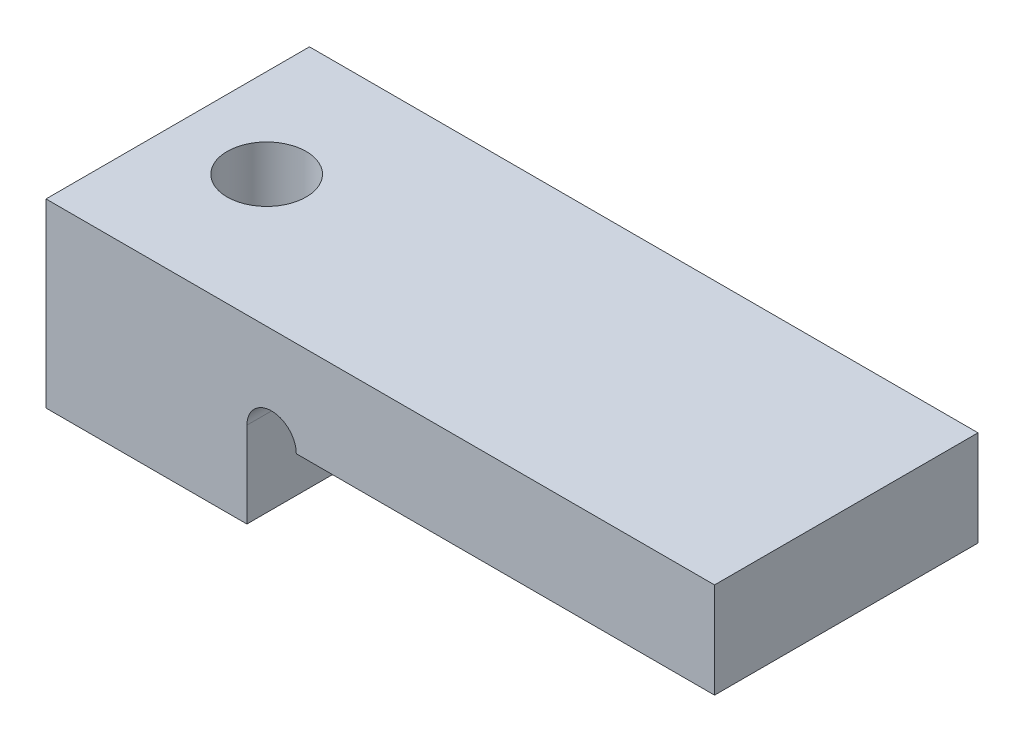
SolidWorks part; units mm, degrees
material "6061-T6 (SS)"
ref_plane "Front Plane" through (0, 0, 0) normal (0, 0, 1) x (1, 0, 0)
ref_plane "Top Plane" through (0, 0, 0) normal (0, 1, 0) x (1, 0, 0)
ref_plane "Right Plane" through (0, 0, 0) normal (1, 0, 0) x (0, 0, -1)
sketch "Sketch1" plane through (0, 0, 0) normal (0, 0, 1) x (1, 0, 0)
  line L4 (0, 0) -> (6.1, 0)
  line L17 (6.1, 2.6) -> (6.1, 0)
  line L21 (6.1, 2.6) -> (20.3, 2.6)
  line L23 (20.3, 5.5) -> (20.3, 2.6)
  line L24 (0, 0) -> (0, 5.5)
  line L25 (20.3, 5.5) -> (0, 5.5)
  dimension "D3" = 6.1
  dimension "D4" = 5.5
  dimension "D6" = 14.2
  dimension "D10" = 2.6
extrude "Boss-Extrude2" add sketch "Sketch1" along normal mid plane 8
sketch "Sketch2" plane through (0, 0, 0) normal (0, 1, 0) x (1, 0, 0)
  line L0 (0, 0) -> (2.7, 0) construction
  line L1 (0, -4) -> (0, 4) construction
  circle A0 centre (2.7, 0) radius 1.2
  dimension "D1" = 2.4
  dimension "D2" = 2.7
extrude "Cut-Extrude2" cut sketch "Sketch2" against normal through all and the other way through all
sketch "Sketch3" plane through (0, 0, 0) normal (0, 0, 1) x (1, 0, 0)
  line L0 (6.1, 2.6) -> (20.3, 2.6) construction
  circle A0 centre (6.85, 2.6) radius 0.75
  dimension "D1" = 1.5
extrude "Cut-Extrude3" cut sketch "Sketch3" against normal through all both and the other way through all
